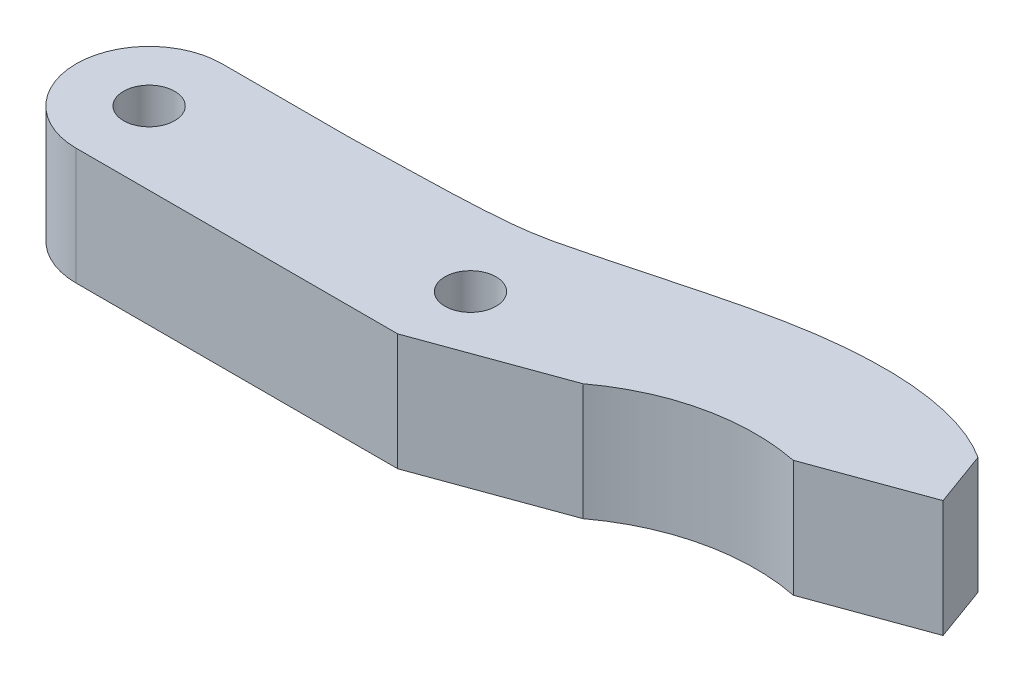
SolidWorks part; units mm, degrees
ref_plane "Ön Düzlem" through (0, 0, 0) normal (0, 0, 1) x (1, 0, 0)
ref_plane "Üst Düzlem" through (0, 0, 0) normal (0, 1, 0) x (1, 0, 0)
ref_plane "Sağ Düzlem" through (0, 0, 0) normal (1, 0, 0) x (0, 0, -1)
sketch "Çizim1" plane through (0, 0, 0) normal (0, 1, 0) x (1, 0, 0)
  line L0 (-55, 0) -> (55, 0) construction
  line L1 (0, -5) -> (22.0155, -5)
  line L2 (0, 5) -> (8.7, 5)
  line L3 (22.0155, -5) -> (31.3184, -1.614)
  line L4 (43.0522, 1.0454) -> (50.5697, 3.7816)
  line L5 (50.5697, 3.7816) -> (49.2017, 7.5404)
  circle A0 centre (0, 0) radius 1.75
  arc A1 (0, 5) -> (0, -5) centre (0, 0) ccw
  circle A2 centre (22, 0) radius 1.75
  arc A3 (31.3184, -1.614) -> (43.0522, 1.0454) centre (40.1743, -13.472) cw
  spline S0 degree 3 poles (8.7, 5) (11.8312, 5.1133) (19.0153, 5.1134) (26.7016, 6.9903) (30.5663, 8.1652) (40.8784, 10.3158) (46.2595, 9.4415) (49.2017, 7.5404) knots 0 0 0 0 0.110725 0.152621 0.389361 0.477058 1 1 1 1
  dimension "D1" = 10
  dimension "D2" = 3.5
  dimension "D4" = 3.5
  dimension "D3" = 22
  dimension "D5" = 8.7
  dimension "D6" = 160
  dimension "D7" = 9.9
  dimension "D8" = 8
  dimension "D9" = 4
extrude "Yükseklik-Ekstrüzyon1" add sketch "Çizim1" along normal blind 8
